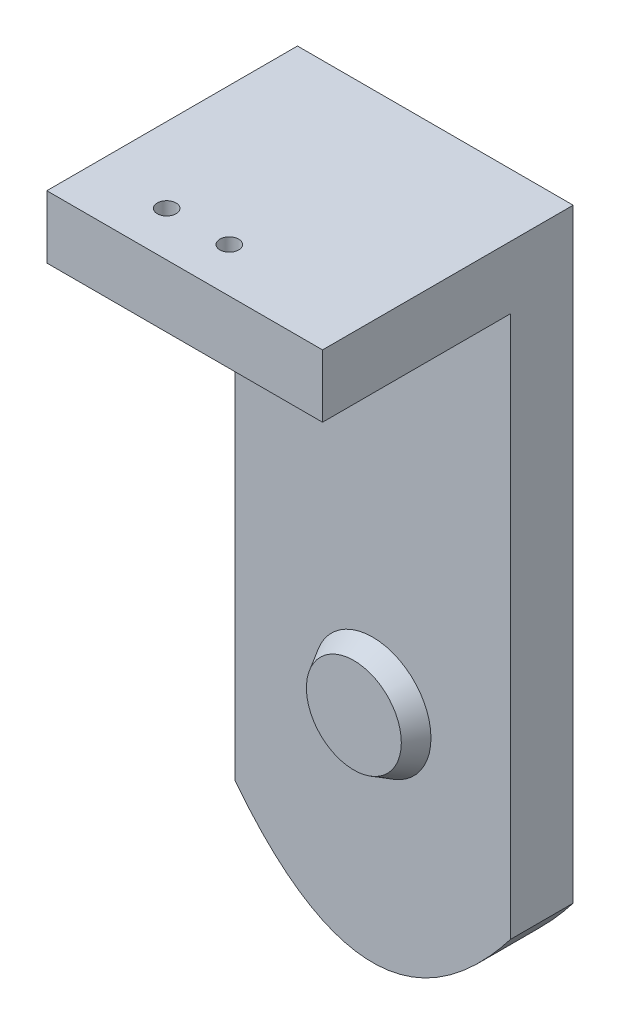
SolidWorks part; units mm, degrees
ref_plane "前视基准面" through (0, 0, 0) normal (0, 0, 1) x (1, 0, 0)
ref_plane "上视基准面" through (0, 0, 0) normal (0, 1, 0) x (1, 0, 0)
ref_plane "右视基准面" through (0, 0, 0) normal (1, 0, 0) x (0, 0, -1)
sketch "草图1" plane through (0, 0, 0) normal (0, 0, 1) x (1, 0, 0)
  circle A0 centre (0, 0) radius 6
  dimension "D1" = 12
sketch "草图2" plane through (0, 0, 0) normal (0, 0, 1) x (1, 0, 0)
  line L0 (0, 0) -> (0, 75) construction
  line L1 (-22, 75) -> (22, 75)
  line L2 (22, 75) -> (22, -21.4718)
  line L3 (-22, 75) -> (-22, -21.4718)
  spline S0 degree 2 poles (-22, -21.4718) (0, -49.8992) (22, -21.4718) knots 0 0 0 1 1 1
  point P5 (0, 75)
  dimension "D1" = 75
  dimension "D2" = 44
extrude "凸台-拉伸1" add sketch "草图2" along normal blind 10 contours L1 L2 S0 L3
extrude "切除-拉伸1" cut sketch "草图1" along normal blind 23 contours A0
sketch "草图3" plane through (0, 0, 10) normal (0, 0, 1) x (1, 0, 0)
  line L0 (22, 75) -> (22, -21.4718) construction
  line L1 (-22, 75) -> (22, 75)
  line L2 (-22, 75) -> (-22, 65)
  line L3 (-22, 65) -> (22, 65)
  line L4 (22, 75) -> (22, 65)
  dimension "D1" = 10
extrude "凸台-拉伸2" add sketch "草图3" along normal blind 30 contours L3 L4 L1 L2
sketch "草图4" plane through (0, 75, 0) normal (0, 1, 0) x (1, 0, 0)
  circle A0 centre (0, -32.8751) radius 1.5
  dimension "D1" = 3
extrude "切除-拉伸2" cut sketch "草图4" against normal blind 15 contours A0
pattern_linear "阵列(线性)1" count 2 spacing 10 along (-1, 0, 0) of "切除-拉伸2"
sketch "草图5" plane through (0, 0, 10) normal (0, 0, 1) x (1, 0, 0)
  circle A0 centre (0, 0) radius 7.5737
extrude "凸台-拉伸3" add sketch "草图5" along normal blind 3 contours A0
draft "拔模1" type of draft neutral plane draft angle 30 faces to draft 1 face at (7.5737, 0, 13) neutral plane through (0, 0, 13) neutral plane normal (0, 0, 1) parameters "D1"=30
